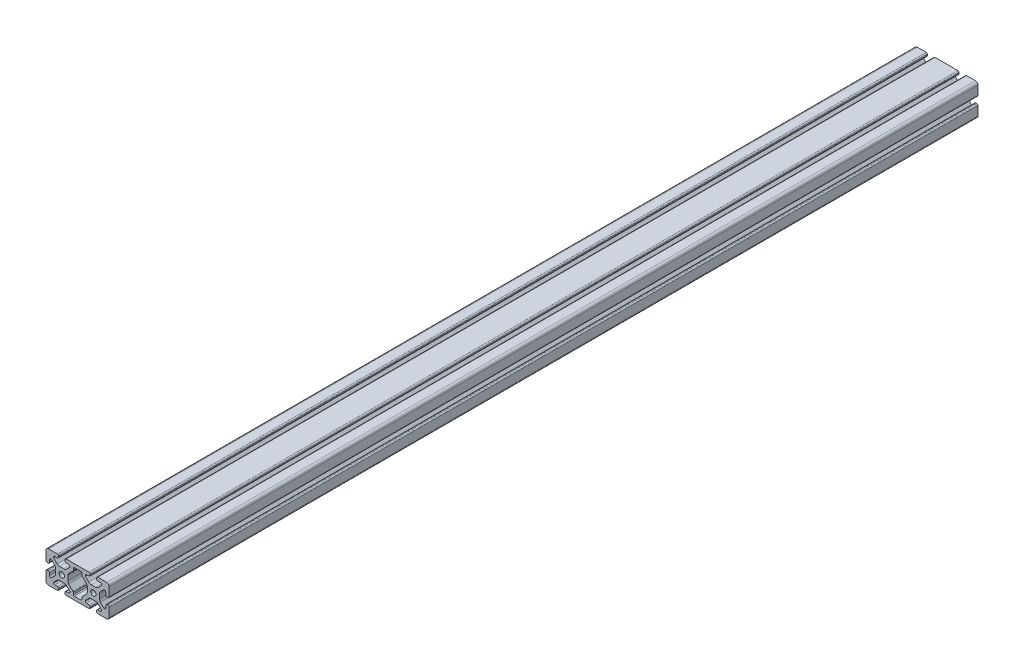
SolidWorks part; units mm, degrees
ref_plane "Front Plane" through (0, 0, 0) normal (0, 0, 1) x (1, 0, 0)
ref_plane "Top Plane" through (0, 0, 0) normal (0, 1, 0) x (1, 0, 0)
ref_plane "Right Plane" through (0, 0, 0) normal (1, 0, 0) x (0, 0, -1)
sketch "Sketch1" plane through (0, 0, 0) normal (0, 0, 1) x (1, 0, 0)
  line L0 (-14.3719, 20) -> (14.3719, 20)
  line L1 (-15.94, 17.1729) -> (-15.94, 18.3529)
  line L2 (-11.285, 15.68) -> (-14.37, 15.68)
  line L3 (-9.715, 13.6545) -> (-9.715, 14.11)
  line L4 (4.0718, 15.68) -> (-4.0718, 15.68)
  line L5 (-5.3418, 14.41) -> (-5.3418, 12.1296)
  line L6 (-5.7137, 11.2316) -> (-10.5988, 6.3465)
  line L7 (-12.2841, 3.2591) -> (-12.2841, -2.725)
  line L8 (5.991, -20) -> (-1.7801, -20)
  line L9 (0, 15.68) -> (0, -15.68) construction
  line L10 (-4.0718, -15.68) -> (4.0718, -15.68)
  line L11 (-5.3418, -12.1296) -> (-5.3418, -14.41)
  line L12 (-11.2012, -5.7441) -> (-5.7137, -11.2316)
  line L13 (-42.275, 0) -> (43.1806, 0) construction
  line L14 (-9.9376, 13.1171) -> (-14.0919, 8.9628)
  line L15 (-17.4506, 7.7) -> (-22.5494, 7.7)
  line L16 (-25.9081, 8.9628) -> (-30.0624, 13.1171)
  line L17 (-30.285, 13.6545) -> (-30.285, 14.11)
  line L18 (-28.715, 15.68) -> (-25.63, 15.68)
  line L19 (-24.06, 17.25) -> (-24.06, 18.4312)
  line L20 (-25.5696, 20) -> (-33, 20)
  line L21 (-33, 20) -> (-36.83, 20)
  line L22 (-40, 16.8406) -> (-40, 13.0106)
  line L23 (-40, 13.0106) -> (-40, 5.5825)
  line L24 (-38.3243, 4.06) -> (-37.1443, 4.06)
  line L25 (-35.68, 5.6264) -> (-35.68, 8.7114)
  line L26 (-34.11, 10.2814) -> (-33.6509, 10.2814)
  line L27 (-33.1135, 10.0588) -> (-29.0111, 5.9564)
  line L28 (-27.7159, 2.571) -> (-27.7159, -2.502)
  line L29 (-28.9155, -5.8608) -> (-33.1719, -10.1172)
  line L30 (-33.7093, -10.3398) -> (-34.111, -10.3398)
  line L31 (-35.68, -8.715) -> (-35.68, -5.63)
  line L32 (-37.25, -4.06) -> (-38.43, -4.06)
  line L33 (-40, -5.5696) -> (-40, -13)
  line L34 (-40, -13) -> (-40, -16.83)
  line L35 (-37.0574, -20) -> (-33.2274, -20)
  line L36 (-33.2274, -20) -> (-25.797, -20)
  line L37 (-24.06, -18.4389) -> (-24.06, -17.25)
  line L38 (-25.63, -15.68) -> (-28.715, -15.68)
  line L39 (-30.285, -14.11) -> (-30.285, -13.6545)
  line L40 (-30.0624, -13.1171) -> (-26.3095, -9.3642)
  line L41 (-23.3415, -7.7) -> (-16.6585, -7.7)
  line L42 (-13.6905, -9.3642) -> (-9.9376, -13.1171)
  line L43 (-9.715, -13.6545) -> (-9.715, -14.11)
  line L44 (-11.285, -15.68) -> (-14.37, -15.68)
  line L45 (-15.94, -17.25) -> (-15.94, -18.43)
  line L46 (-14.37, -20) -> (-5.991, -20)
  line L47 (-5.991, -20) -> (-1.7801, -20)
  line L48 (14.37, -20) -> (5.991, -20)
  line L49 (15.94, -17.25) -> (15.94, -18.43)
  line L50 (11.285, -15.68) -> (14.37, -15.68)
  line L51 (9.715, -13.6545) -> (9.715, -14.11)
  line L52 (13.6905, -9.3642) -> (9.9376, -13.1171)
  line L53 (23.3415, -7.7) -> (16.6585, -7.7)
  line L54 (30.0624, -13.1171) -> (26.3095, -9.3642)
  line L55 (30.285, -14.11) -> (30.285, -13.6545)
  line L56 (25.63, -15.68) -> (28.715, -15.68)
  line L57 (24.06, -18.4389) -> (24.06, -17.25)
  line L58 (33.2274, -20) -> (25.797, -20)
  line L59 (37.0574, -20) -> (33.2274, -20)
  line L60 (40, -13) -> (40, -16.83)
  line L61 (40, -5.5696) -> (40, -13)
  line L62 (37.25, -4.06) -> (38.4312, -4.06)
  line L63 (35.68, -8.715) -> (35.68, -5.63)
  line L64 (33.7093, -10.3398) -> (34.111, -10.3398)
  line L65 (28.9155, -5.8608) -> (33.1719, -10.1172)
  line L66 (27.7159, 2.571) -> (27.7159, -2.502)
  line L67 (33.1135, 10.0588) -> (29.0111, 5.9564)
  line L68 (34.11, 10.2814) -> (33.6509, 10.2814)
  line L69 (35.68, 5.6264) -> (35.68, 8.7114)
  line L70 (38.3243, 4.06) -> (37.1443, 4.06)
  line L71 (40, 13.0106) -> (40, 5.5825)
  line L72 (40, 16.8406) -> (40, 13.0106)
  line L73 (33, 20) -> (36.83, 20)
  line L74 (25.5696, 20) -> (33, 20)
  line L75 (24.06, 17.25) -> (24.06, 18.4312)
  line L76 (28.715, 15.68) -> (25.63, 15.68)
  line L77 (30.285, 13.6545) -> (30.285, 14.11)
  line L78 (25.9081, 8.9628) -> (30.0624, 13.1171)
  line L79 (17.4506, 7.7) -> (22.5494, 7.7)
  line L80 (9.9376, 13.1171) -> (14.0919, 8.9628)
  line L81 (11.2012, -5.7441) -> (5.7137, -11.2316)
  line L82 (5.3418, -12.1296) -> (5.3418, -14.41)
  line L83 (12.2841, 3.2591) -> (12.2841, -2.725)
  line L84 (5.7137, 11.2316) -> (10.5988, 6.3465)
  line L85 (5.3418, 14.41) -> (5.3418, 12.1296)
  line L86 (9.715, 13.6545) -> (9.715, 14.11)
  line L87 (11.285, 15.68) -> (14.37, 15.68)
  line L88 (15.94, 17.1729) -> (15.94, 18.3529)
  line L89 (-20, 24.8708) -> (-20, -18.43) construction
  line L90 (20, 29.4355) -> (20, -23.1087) construction
  line L91 (-3.0962, 16.9038) -> (-43.6857, -23.6857) construction
  line L92 (-36.2671, 16.2671) -> (-2.7875, -17.2125) construction
  arc A0 (-15.94, 18.3529) -> (-14.3719, 20) centre (-14.3719, 18.43) cw
  circle A1 centre (-20, 0) radius 3.4
  arc A2 (-14.37, 15.68) -> (-15.94, 17.1729) centre (-14.3719, 17.25) cw
  arc A3 (-11.285, 15.68) -> (-9.715, 14.11) centre (-11.285, 14.11) cw
  arc A4 (-9.715, 13.6545) -> (-9.9376, 13.1171) centre (-10.475, 13.6545) cw
  arc A5 (-12.2841, -2.725) -> (-11.2012, -5.7441) centre (-7.5341, -2.725) ccw
  arc A6 (-4.0718, 15.68) -> (-5.3418, 14.41) centre (-4.0718, 14.41) ccw
  arc A7 (-5.7137, 11.2316) -> (-5.3418, 12.1296) centre (-6.6118, 12.1296) ccw
  arc A8 (-10.5988, 6.3465) -> (-12.2841, 3.2591) centre (-7.5685, 2.6887) ccw
  arc A9 (-5.3418, -14.41) -> (-4.0718, -15.68) centre (-4.0718, -14.41) ccw
  arc A10 (-5.3418, -12.1296) -> (-5.7137, -11.2316) centre (-6.6118, -12.1296) ccw
  arc A11 (-17.4506, 7.7) -> (-14.0919, 8.9628) centre (-17.3191, 12.4482) ccw
  arc A12 (-25.9081, 8.9628) -> (-22.5494, 7.7) centre (-22.6809, 12.4482) ccw
  arc A13 (-30.285, 13.6545) -> (-30.0624, 13.1171) centre (-29.525, 13.6545) ccw
  arc A14 (-28.715, 15.68) -> (-30.285, 14.11) centre (-28.715, 14.11) ccw
  arc A15 (-25.63, 15.68) -> (-24.06, 17.25) centre (-25.63, 17.25) ccw
  arc A16 (-24.06, 18.4312) -> (-25.5696, 20) centre (-25.63, 18.4312) ccw
  arc A17 (-36.83, 20) -> (-40, 16.8406) centre (-36.83, 16.83) ccw
  arc A18 (-40, 5.5825) -> (-38.3243, 4.06) centre (-38.4306, 5.6264) ccw
  arc A19 (-37.1443, 4.06) -> (-35.68, 5.6264) centre (-37.25, 5.6264) ccw
  arc A20 (-34.11, 10.2814) -> (-35.68, 8.7114) centre (-34.11, 8.7114) ccw
  arc A21 (-33.1135, 10.0588) -> (-33.6509, 10.2814) centre (-33.6509, 9.5214) ccw
  arc A22 (-27.7159, 2.571) -> (-29.0111, 5.9564) centre (-32.4643, 2.6948) ccw
  arc A23 (-28.9155, -5.8608) -> (-27.7159, -2.502) centre (-32.4617, -2.7006) ccw
  arc A24 (-33.7093, -10.3398) -> (-33.1719, -10.1172) centre (-33.7093, -9.5798) ccw
  arc A25 (-35.68, -8.715) -> (-34.111, -10.3398) centre (-34.111, -8.7698) ccw
  arc A26 (-35.68, -5.63) -> (-37.25, -4.06) centre (-37.25, -5.63) ccw
  arc A27 (-38.43, -4.06) -> (-40, -5.5696) centre (-38.4312, -5.63) ccw
  arc A28 (-40, -16.83) -> (-37.0574, -20) centre (-36.83, -16.8382) ccw
  arc A29 (-25.797, -20) -> (-24.06, -18.4389) centre (-25.63, -18.4389) ccw
  arc A30 (-24.06, -17.25) -> (-25.63, -15.68) centre (-25.63, -17.25) ccw
  arc A31 (-30.285, -14.11) -> (-28.715, -15.68) centre (-28.715, -14.11) ccw
  arc A32 (-30.0624, -13.1171) -> (-30.285, -13.6545) centre (-29.525, -13.6545) ccw
  arc A33 (-23.3415, -7.7) -> (-26.3095, -9.3642) centre (-22.6565, -12.4003) ccw
  arc A34 (-13.6905, -9.3642) -> (-16.6585, -7.7) centre (-17.3435, -12.4003) ccw
  arc A35 (-9.715, -13.6545) -> (-9.9376, -13.1171) centre (-10.475, -13.6545) ccw
  arc A36 (-11.285, -15.68) -> (-9.715, -14.11) centre (-11.285, -14.11) ccw
  arc A37 (-14.37, -15.68) -> (-15.94, -17.25) centre (-14.37, -17.25) ccw
  arc A38 (-15.94, -18.43) -> (-14.37, -20) centre (-14.37, -18.43) ccw
  arc A39 (15.94, -18.43) -> (14.37, -20) centre (14.37, -18.43) cw
  arc A40 (14.37, -15.68) -> (15.94, -17.25) centre (14.37, -17.25) cw
  arc A41 (11.285, -15.68) -> (9.715, -14.11) centre (11.285, -14.11) cw
  arc A42 (9.715, -13.6545) -> (9.9376, -13.1171) centre (10.475, -13.6545) cw
  arc A43 (13.6905, -9.3642) -> (16.6585, -7.7) centre (17.3435, -12.4003) cw
  arc A44 (23.3415, -7.7) -> (26.3095, -9.3642) centre (22.6565, -12.4003) cw
  arc A45 (30.0624, -13.1171) -> (30.285, -13.6545) centre (29.525, -13.6545) cw
  arc A46 (30.285, -14.11) -> (28.715, -15.68) centre (28.715, -14.11) cw
  arc A47 (24.06, -17.25) -> (25.63, -15.68) centre (25.63, -17.25) cw
  arc A48 (25.797, -20) -> (24.06, -18.4389) centre (25.63, -18.4389) cw
  arc A49 (40, -16.83) -> (37.0574, -20) centre (36.83, -16.8382) cw
  arc A50 (38.4312, -4.06) -> (40, -5.5696) centre (38.4312, -5.63) cw
  arc A51 (35.68, -5.63) -> (37.25, -4.06) centre (37.25, -5.63) cw
  arc A52 (35.68, -8.715) -> (34.111, -10.3398) centre (34.111, -8.7698) cw
  arc A53 (33.7093, -10.3398) -> (33.1719, -10.1172) centre (33.7093, -9.5798) cw
  arc A54 (28.9155, -5.8608) -> (27.7159, -2.502) centre (32.4617, -2.7006) cw
  arc A55 (27.7159, 2.571) -> (29.0111, 5.9564) centre (32.4643, 2.6948) cw
  arc A56 (33.1135, 10.0588) -> (33.6509, 10.2814) centre (33.6509, 9.5214) cw
  arc A57 (34.11, 10.2814) -> (35.68, 8.7114) centre (34.11, 8.7114) cw
  arc A58 (37.1443, 4.06) -> (35.68, 5.6264) centre (37.25, 5.6264) cw
  arc A59 (40, 5.5825) -> (38.3243, 4.06) centre (38.4306, 5.6264) cw
  arc A60 (36.83, 20) -> (40, 16.8406) centre (36.83, 16.83) cw
  arc A61 (24.06, 18.4312) -> (25.5696, 20) centre (25.63, 18.4312) cw
  arc A62 (25.63, 15.68) -> (24.06, 17.25) centre (25.63, 17.25) cw
  arc A63 (28.715, 15.68) -> (30.285, 14.11) centre (28.715, 14.11) cw
  arc A64 (30.285, 13.6545) -> (30.0624, 13.1171) centre (29.525, 13.6545) cw
  arc A65 (25.9081, 8.9628) -> (22.5494, 7.7) centre (22.6809, 12.4482) cw
  arc A66 (17.4506, 7.7) -> (14.0919, 8.9628) centre (17.3191, 12.4482) cw
  arc A67 (5.3418, -12.1296) -> (5.7137, -11.2316) centre (6.6118, -12.1296) cw
  arc A68 (5.3418, -14.41) -> (4.0718, -15.68) centre (4.0718, -14.41) cw
  arc A69 (10.5988, 6.3465) -> (12.2841, 3.2591) centre (7.5685, 2.6887) cw
  arc A70 (5.7137, 11.2316) -> (5.3418, 12.1296) centre (6.6118, 12.1296) cw
  arc A71 (4.0718, 15.68) -> (5.3418, 14.41) centre (4.0718, 14.41) cw
  arc A72 (12.2841, -2.725) -> (11.2012, -5.7441) centre (7.5341, -2.725) cw
  arc A73 (9.715, 13.6545) -> (9.9376, 13.1171) centre (10.475, 13.6545) ccw
  arc A74 (11.285, 15.68) -> (9.715, 14.11) centre (11.285, 14.11) ccw
  arc A75 (14.37, 15.68) -> (15.94, 17.1729) centre (14.3719, 17.25) ccw
  circle A76 centre (20, 0) radius 3.4
  arc A77 (15.94, 18.3529) -> (14.3719, 20) centre (14.3719, 18.43) ccw
  dimension "D4" = 6.8
  dimension "D1" = 80
  dimension "D2" = 40
  dimension "D3" = 20
  dimension "D5" = 8.12
  dimension "D6" = 4.32
  dimension "D7" = 20.57
  dimension "D8" = 4.32
  dimension "D9" = 12.3
  dimension "D10" = 8.12
  dimension "D11" = 4.32
  dimension "D12" = 4.32
  dimension "D13" = 4.32
extrude "Boss-Extrude1" add sketch "Sketch1" along normal blind 1100
